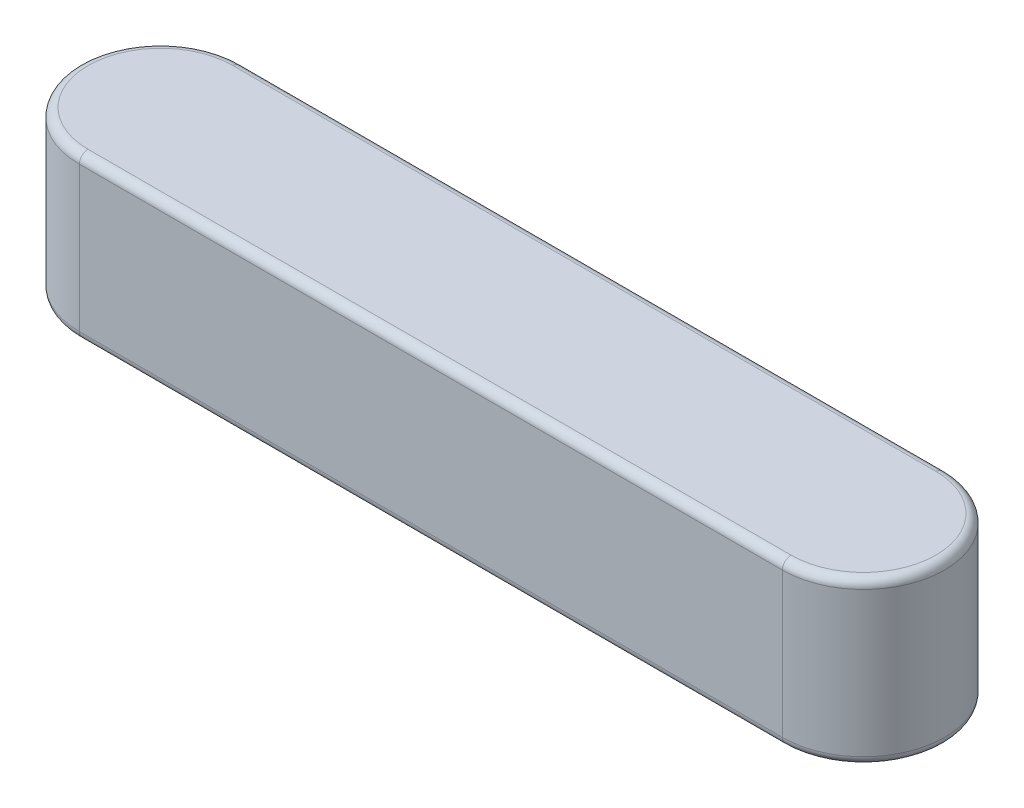
SolidWorks part; units mm, degrees
ref_plane "Front Plane" through (0, 0, 0) normal (0, 0, 1) x (1, 0, 0)
ref_plane "Top Plane" through (0, 0, 0) normal (0, 1, 0) x (1, 0, 0)
ref_plane "Right Plane" through (0, 0, 0) normal (1, 0, 0) x (0, 0, -1)
sketch "Sketch1" plane through (0, 0, 0) normal (0, 1, 0) x (1, 0, 0)
  line L1 (-13, 1.5) -> (0, 1.5)
  line L3 (-13, -1.5) -> (0, -1.5)
  arc A0 (0, -1.5) -> (0, 1.5) centre (0, 0) ccw
  arc A1 (-13, 1.5) -> (-13, -1.5) centre (-13, 0) ccw
  dimension "l" = 16
  dimension "b" = 3
extrude "Extrude1" add sketch "Sketch1" along normal blind 3
fillet "Fillet1" radius 0.16 8 edges at (-6.5, 0, -1.5) (1.5, 0, 0) (-14.5, 0, 0) (-6.5, 0, 1.5) (1.5, 3, 0) (-6.5, 3, 1.5) (-6.5, 3, -1.5) (-14.5, 3, 0)
